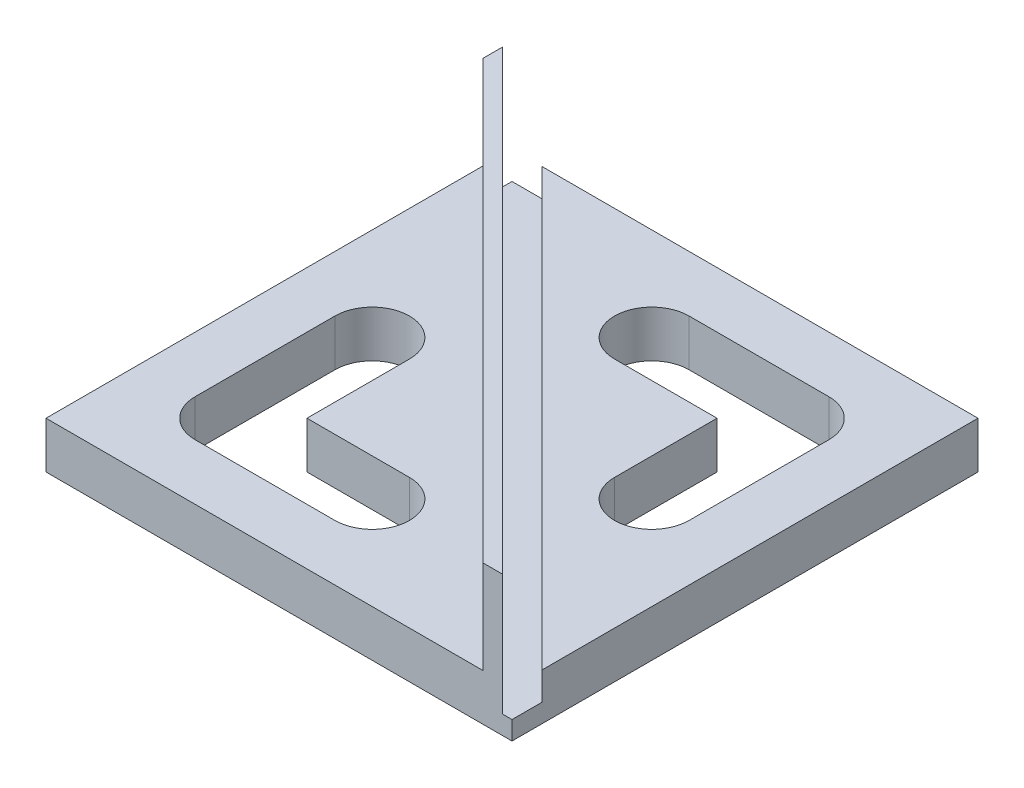
SolidWorks part; units mm, degrees
ref_plane "Front Plane" through (0, 0, 0) normal (0, 0, 1) x (1, 0, 0)
ref_plane "Top Plane" through (0, 0, 0) normal (0, 1, 0) x (1, 0, 0)
ref_plane "Right Plane" through (0, 0, 0) normal (1, 0, 0) x (0, 0, -1)
sketch "Sketch1" plane through (0, 0, 0) normal (0, 1, 0) x (1, 0, 0)
  line L0 (15, 19) -> (0, 19)
  line L1 (-25, 25) -> (25, 25)
  line L2 (-25, 25) -> (-25, -25)
  line L3 (-25, -25) -> (25, -25)
  line L4 (25, 25) -> (25, -25)
  line L5 (-25, 25) -> (25, -25) construction
  line L6 (-25, -25) -> (25, 25) construction
  line L7 (0, 11) -> (11, 11)
  line L8 (11, 11) -> (11, 0)
  line L9 (19, 0) -> (19, 15)
  line L10 (-15, -19) -> (0, -19)
  line L11 (0, -11) -> (-11, -11)
  line L12 (-11, -11) -> (-11, 0)
  line L13 (-19, 0) -> (-19, -15)
  arc A0 (19, 15) -> (15, 19) centre (15, 15) ccw
  arc A1 (0, 19) -> (0, 11) centre (0, 15) ccw
  arc A2 (11, 0) -> (19, 0) centre (15, 0) ccw
  arc A3 (-19, -15) -> (-15, -19) centre (-15, -15) ccw
  arc A4 (0, -19) -> (0, -11) centre (0, -15) ccw
  arc A5 (-11, 0) -> (-19, 0) centre (-15, 0) ccw
  point P0 (0, 0)
  point P7 (0, 0)
  dimension "D3" = 8
  dimension "D12" = 4
  dimension "D13" = 4
  dimension "D5" = 4
  dimension "D14" = 90
  dimension "D1" = 50
  dimension "D2" = 50
  dimension "D4" = 10
  dimension "D6" = 15
  dimension "D7" = 15
  dimension "D8" = 4
  dimension "D9" = 10
  dimension "D10" = 10
  dimension "D11" = 8
  dimension "D15" = 15
  dimension "D16" = 15
extrude "Boss-Extrude1" add sketch "Sketch1" along normal blind 5
sketch "Sketch2" plane through (0, 5, 0) normal (0, 1, 0) x (1, 0, 0)
  line L0 (-25, 21.8787) -> (21.8787, -25)
  line L1 (-25, 25) -> (-25, -25) construction
  line L2 (-25, -25) -> (25, -25) construction
  line L3 (21.8787, -25) -> (24, -25)
  line L4 (24, -25) -> (-25, 24)
  line L5 (-25, 24) -> (-25, 21.8787)
  line L6 (25, 25) -> (-25, 25) construction
  dimension "D1" = 45
  dimension "D2" = 1.5
  dimension "D3" = 1
extrude "Boss-Extrude2" add sketch "Sketch2" along normal blind 10
sketch "Sketch3" plane through (0, 5, 0) normal (0, 1, 0) x (1, 0, 0)
  line L0 (-21.7574, 25) -> (25, -21.7574)
  line L1 (25, 25) -> (-25, 25) construction
  line L2 (25, -25) -> (25, 25) construction
  line L3 (25, -21.7574) -> (25, -25)
  line L4 (25, -25) -> (24, -25)
  line L5 (24, -25) -> (-25, 24)
  line L6 (-25, 24) -> (-25, 25)
  line L7 (-25, 25) -> (-21.7574, 25)
  dimension "D1" = 3
extrude "Cut-Extrude1" cut sketch "Sketch3" against normal blind 3
sketch "Sketch4" plane through (-1.5607, 0, 1.5607) normal (-0.7071, 0, 0.7071) x (0.7071, 0, 0.7071)
  line L0 (-33.1482, 15) -> (-33.1482, 5) construction
  line L2 (-31.1482, 10) -> (29.3518, 10) construction
  line L3 (29.3518, 10) -> (37.3121, 9.5625) construction
  circle A0 centre (-31.1482, 10) radius 1.65
  circle A1 centre (23.8518, 10) radius 1.65
  circle A2 centre (29.3518, 10) radius 1.65
  circle A3 centre (-25.6482, 10) radius 1.65
  dimension "D1" = 3.3
  dimension "D2" = 3.3
  dimension "D5" = 3.3
  dimension "D6" = 3.3
  dimension "D3" = 55
  dimension "D4" = 2
  dimension "D8" = 5.5
  dimension "D9" = 5.5
extrude "Cut-Extrude2" cut sketch "Sketch4" against normal through all
